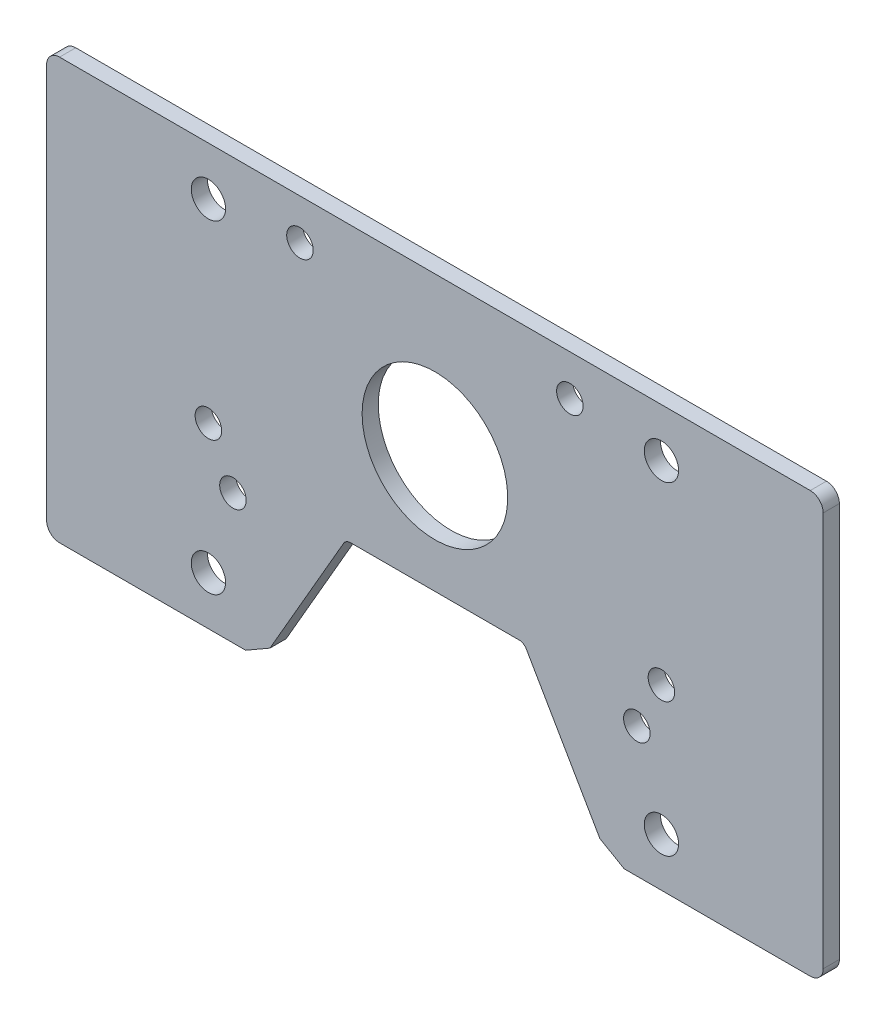
SolidWorks part; units mm, degrees
ref_plane "Front Plane" through (0, 0, 0) normal (0, 0, 1) x (1, 0, 0)
ref_plane "Top Plane" through (0, 0, 0) normal (0, 1, 0) x (1, 0, 0)
ref_plane "Right Plane" through (0, 0, 0) normal (1, 0, 0) x (0, 0, -1)
ref_plane "Plane1" through (0, 0, 3.175) normal (0, 0, 1) x (1, 0, 0)
sketch "Sketch1" plane through (0, 0, 3.175) normal (0, 0, 1) x (1, 0, 0)
  line L0 (53.975, -25.4) -> (53.975, 50.8)
  line L1 (53.975, 50.8) -> (50.8, 53.975)
  line L2 (50.8, 53.975) -> (-50.8, 53.975)
  line L3 (-50.8, 53.975) -> (-53.975, 50.8)
  line L4 (-53.975, 50.8) -> (-53.975, -25.4)
  line L5 (-53.975, -25.4) -> (-50.8, -28.575)
  line L6 (-50.8, -28.575) -> (-37.1353, -28.575)
  line L7 (-37.1353, -28.575) -> (-32.3728, -25.8254)
  line L8 (-32.3728, -25.8254) -> (-17.9208, -0.7938)
  line L9 (-16.546, 0) -> (16.546, 0)
  line L10 (17.9208, -0.7937) -> (32.3728, -25.8254)
  line L11 (32.3728, -25.8254) -> (37.1353, -28.575)
  line L12 (37.1353, -28.575) -> (50.8, -28.575)
  line L13 (50.8, -28.575) -> (53.975, -25.4)
  circle A0 centre (44.45, 6.35) radius 2.6035
  circle A1 centre (26.4841, 46.0057) radius 2.6035
  circle A2 centre (-39.6321, -3.0633) radius 2.6035
  circle A3 centre (44.45, -19.05) radius 3.3655
  circle A4 centre (44.45, 44.45) radius 3.3655
  circle A5 centre (0, 23.0587) radius 14.2875
  arc A6 (-17.9208, -0.7938) -> (-16.546, 0) centre (-16.546, -1.5875) cw
  arc A7 (16.546, 0) -> (17.9208, -0.7937) centre (16.546, -1.5875) cw
  circle A8 centre (-44.45, 44.45) radius 3.3655
  circle A9 centre (-44.45, -19.05) radius 3.3655
  circle A10 centre (-44.45, 6.35) radius 2.6035
  circle A11 centre (-26.4841, 46.0057) radius 2.6035
  circle A12 centre (39.6321, -3.0633) radius 2.6035
extrude "Boss-Extrude1" add sketch "Sketch1" against normal blind 3.175
sketch "Sketch2" plane through (0, 0, 3.175) normal (0, 0, 1) x (1, 0, 0)
  line L0 (-50.8, 53.975) -> (-76.2, 53.975)
  line L1 (-76.2, 53.975) -> (-76.2, -28.575)
  line L2 (-76.2, -28.575) -> (-50.8, -28.575)
  line L3 (-50.8, -28.575) -> (-50.8, 53.975)
  line L4 (0, 53.975) -> (0, 0) construction
  line L5 (50.8, 53.975) -> (-50.8, 53.975) construction
  line L6 (-16.546, 0) -> (16.546, 0) construction
  line L7 (50.8, -28.575) -> (50.8, 53.975)
  line L8 (76.2, -28.575) -> (50.8, -28.575)
  line L9 (76.2, 53.975) -> (76.2, -28.575)
  line L10 (50.8, 53.975) -> (76.2, 53.975)
  dimension "D1" = 25.4
extrude "Boss-Extrude2" add sketch "Sketch2" against normal through all
fillet "Fillet1" radius 2.54 4 edges at (76.2, 53.975, 1.5875) (76.2, -28.575, 1.5875) (-76.2, -28.575, 1.5875) (-76.2, 53.975, 1.5875)
